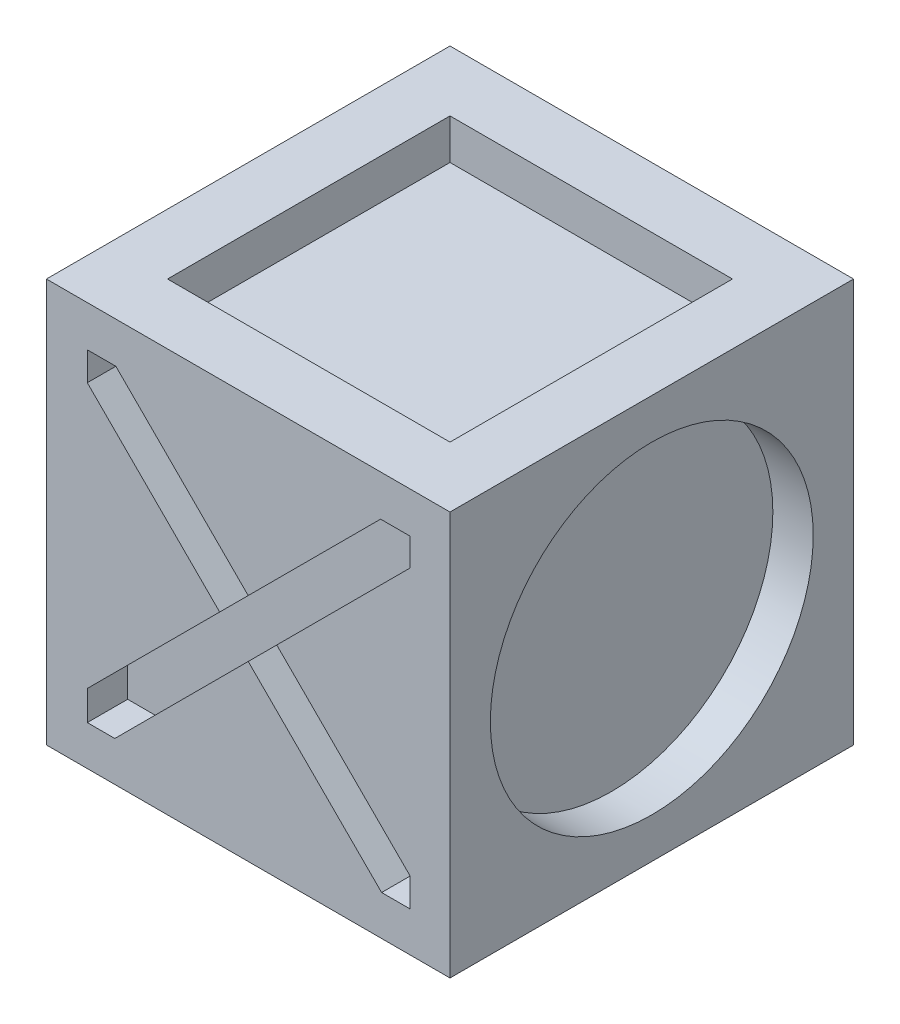
SolidWorks part; units mm, degrees
ref_plane "Front Plane" through (0, 0, 0) normal (0, 0, 1) x (1, 0, 0)
ref_plane "Top Plane" through (0, 0, 0) normal (0, 1, 0) x (1, 0, 0)
ref_plane "Right Plane" through (0, 0, 0) normal (1, 0, 0) x (0, 0, -1)
sketch "Sketch2" plane through (0, 0, 0) normal (0, 1, 0) x (1, 0, 0)
  line L1 (0, 0) -> (10, 0)
  line L2 (0, 0) -> (0, 10)
  line L3 (0, 10) -> (10, 10)
  line L4 (10, 0) -> (10, 10)
extrude "Boss-Extrude1" add sketch "Sketch2" along normal blind 10
sketch "Sketch3" plane through (0, 0, 0) normal (0, 0, 1) x (1, 0, 0)
  line L0 (8.3056, 0.9873) -> (9.0127, 0.9873)
  line L2 (4.2929, 5) -> (1.0127, 8.2802)
  line L14 (4.2929, 5) -> (1.0127, 1.7198)
  line L16 (5, 5.7071) -> (1.7198, 8.9873)
  line L17 (5, 5.7071) -> (8.2802, 8.9873)
  line L18 (5.7071, 5) -> (9.0127, 8.3056)
  line L19 (5.7071, 5) -> (9.0127, 1.6944)
  line L20 (5, 4.2929) -> (8.3056, 0.9873)
  line L21 (5, 4.2929) -> (1.6944, 0.9873)
  line L22 (1.0127, 8.2802) -> (1.0127, 8.9873)
  line L23 (1.0127, 1.7198) -> (1.0127, 0.9873)
  line L24 (1.0127, 0.9873) -> (1.6944, 0.9873)
  line L25 (9.0127, 0.9873) -> (9.0127, 1.6944)
  line L26 (9.0127, 8.3056) -> (9.0127, 8.9873)
  line L27 (1.0127, 8.9873) -> (1.7198, 8.9873)
  line L28 (8.2802, 8.9873) -> (9.0127, 8.9873)
extrude "Cut-Extrude1" cut sketch "Sketch3" against normal blind 1
sketch "Sketch4" plane through (10, 0, 0) normal (1, 0, 0) x (0, 0, -1)
  circle A1 centre (5, 5) radius 4
extrude "Cut-Extrude2" cut sketch "Sketch4" against normal blind 1
sketch "Sketch5" plane through (0, 10, 0) normal (0, 1, 0) x (1, 0, 0)
  line L3 (8.5, 1.5) -> (1.5, 1.5)
  line L4 (8.5, 1.5) -> (8.5, 8.5)
  line L5 (8.5, 8.5) -> (1.5, 8.5)
  line L6 (1.5, 1.5) -> (1.5, 8.5)
  line L7 (8.5, 1.5) -> (1.5, 8.5) construction
  line L8 (8.5, 8.5) -> (1.5, 1.5) construction
  point P8 (5, 5)
extrude "Cut-Extrude3" cut sketch "Sketch5" against normal blind 1
sketch "Sketch6" plane through (0, 0, -10) normal (0, 0, -1) x (-1, 0, 0)
  line L0 (-7.6913, 8.1699) -> (-1.5961, 6.2921)
  line L1 (-1.5961, 6.2921) -> (-3.9459, 3.6127)
  line L2 (-3.9459, 3.6127) -> (-3.763, 5.8224)
  line L3 (-3.763, 5.8224) -> (-6.1459, 4.3855)
  line L4 (-6.1459, 4.3855) -> (-2.771, 1.8109)
  line L5 (-2.771, 1.8109) -> (-7.5431, 1.4632)
  line L6 (-7.5431, 1.4632) -> (-5.7545, 2.8872)
  line L7 (-5.7545, 2.8872) -> (-8.3222, 4.846)
  line L8 (-8.3222, 4.846) -> (-5.9242, 6.2921)
  line L9 (-5.9242, 6.2921) -> (-7.6913, 8.1699)
extrude "Cut-Extrude4" cut sketch "Sketch6" against normal blind 1
sketch "Sketch7" plane through (0, 0, 0) normal (-1, 0, 0) x (0, 0, 1)
  circle A0 centre (-7.0722, 3.1373) radius 1.3038
  circle A1 centre (-5.5896, 7.1022) radius 2.0536
  circle A2 centre (-2.9801, 3.1373) radius 1.8407
extrude "Cut-Extrude5" cut sketch "Sketch7" against normal blind 1
sketch "Sketch9" plane through (0, 0, 0) normal (0, -1, 0) x (-1, 0, 0)
  line L0 (-9.0415, 5) -> (-7.0207, 1.5)
  line L1 (-2.9793, 1.5) -> (-0.9585, 5)
  line L2 (-2.9793, 8.5) -> (-0.9585, 5)
  line L9 (-2.9793, 1.5) -> (-7.0207, 1.5)
  line L10 (-9.0415, 5) -> (-7.0207, 8.5)
  line L11 (-7.0207, 8.5) -> (-2.9793, 8.5)
extrude "Cut-Extrude13" cut sketch "Sketch9" against normal blind 0.5
